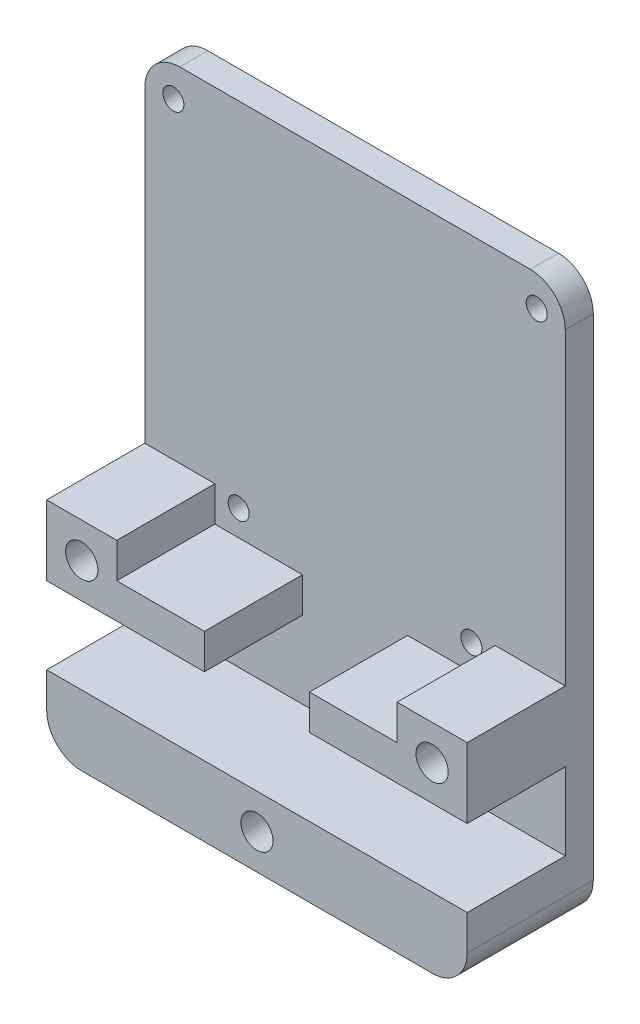
SolidWorks part; units mm, degrees
ref_plane "Plan de face" through (0, 0, 0) normal (0, 0, 1) x (1, 0, 0)
ref_plane "Plan de dessus" through (0, 0, 0) normal (0, 1, 0) x (1, 0, 0)
ref_plane "Plan de droite" through (0, 0, 0) normal (1, 0, 0) x (0, 0, -1)
sketch "Esquisse1" plane through (0, 0, 0) normal (0, 0, 1) x (1, 0, 0)
  line L0 (5, 0) -> (55, 0)
  line L1 (0, -5) -> (0, -75)
  line L2 (60, -5) -> (60, -75)
  line L3 (5, -80) -> (55, -80)
  arc A0 (0, -75) -> (5, -80) centre (5, -75) ccw
  arc A1 (55, -80) -> (60, -75) centre (55, -75) ccw
  arc A2 (60, -5) -> (55, 0) centre (55, -5) ccw
  arc A3 (0, -5) -> (5, 0) centre (5, -5) cw
  point P7 (0, -80)
  point P10 (60, -80)
  point P13 (60, 0)
  point P16 (0, 0)
  dimension "D3" = 5
  dimension "D1" = 60
  dimension "D2" = 80
extrude "Boss.-Extru.1" add sketch "Esquisse1" along normal blind 4 contours L2 A1 L3 A0 L1 A3 L0 A2
sketch "Esquisse2" plane through (0, 0, 4) normal (0, 0, 1) x (1, 0, 0)
  line L2 (5, -80) -> (55, -80)
  line L3 (5, -80) -> (55, -80)
  line L4 (0, -59) -> (60, -59)
  line L5 (0, -5) -> (0, -75) construction
  line L6 (60, -5) -> (60, -75) construction
  line L7 (0, -59) -> (22.5, -59)
  line L8 (0, -59) -> (0, -49)
  line L11 (60, -59) -> (37.5, -59)
  line L12 (60, -59) -> (60, -49)
  line L15 (0, -75) -> (0, -70)
  line L16 (0, -70) -> (60, -70)
  line L17 (60, -70) -> (60, -75)
  line L18 (60, -49) -> (50, -49)
  line L19 (50, -49) -> (50, -54)
  line L20 (50, -54) -> (37.5, -54)
  line L21 (37.5, -54) -> (37.5, -59)
  line L22 (22.5, -59) -> (22.5, -54)
  line L23 (22.5, -54) -> (10, -54)
  line L24 (10, -54) -> (10, -49)
  line L25 (10, -49) -> (0, -49)
  arc A4 (55, -80) -> (60, -75) centre (55, -75) ccw
  arc A5 (0, -75) -> (5, -80) centre (5, -75) ccw
  arc A6 (55, -80) -> (60, -75) centre (55, -75) ccw
  arc A7 (0, -75) -> (5, -80) centre (5, -75) ccw
  dimension "D2" = 10
  dimension "D3" = 10
  dimension "D4" = 10
  dimension "D5" = 90
  dimension "D6" = 10
  dimension "D7" = 10
  dimension "D8" = 11
  dimension "D9" = 5
  dimension "D10" = 5
  dimension "D11" = 15
  dimension "D12" = 22.5
  dimension "D13" = 22.5
  dimension "D1" = 0
extrude "Boss.-Extru.2" add sketch "Esquisse2" along normal blind 14
sketch "Esquisse3" plane through (0, 0, 4) normal (0, 0, 1) x (1, 0, 0)
  line L0 (10, -54) -> (50, -54) construction
  line L1 (22.5, -54) -> (10, -54) construction
  line L2 (60, 0) -> (0, 0) construction
  line L5 (22.5, -54) -> (10, -54) construction
  line L6 (60, 0) -> (60, -6.2547) construction
  line L7 (30, -54) -> (30, 0) construction
  line L8 (60, -5) -> (60, -49) construction
  line L9 (0, 0) -> (0, -7.426) construction
  line L10 (0, -5) -> (0, -49) construction
  line L11 (10, -54) -> (60, 0) construction
  line L12 (0, 0) -> (50, -54) construction
  circle A8 centre (55.9236, -4.4026) radius 1.5
  circle A9 centre (46.603, -50.3312) radius 1.5
  circle A10 centre (4.0764, -4.4026) radius 1.5
  circle A11 centre (13.397, -50.3312) radius 1.5
  dimension "D1" = 3
  dimension "D3" = 3
  dimension "D5" = 30
  dimension "D2" = 6
  dimension "D4" = 5
extrude "Enlèv. mat.-Extru.1" cut sketch "Esquisse3" against normal up to surface (4 mm away) up to face at (30, -40, 0)
sketch "Esquisse4" plane through (0, 0, 18) normal (0, 0, 1) x (1, 0, 0)
  line L0 (50, -49) -> (60, -59) construction
  line L1 (10, -49) -> (0, -59) construction
  line L2 (30, -70) -> (30, -80) construction
  line L3 (0, -70) -> (60, -70) construction
  line L4 (5, -80) -> (55, -80) construction
  circle A0 centre (55, -54) radius 2.3
  circle A1 centre (5, -54) radius 2.3
  circle A2 centre (30, -75) radius 2.3
  dimension "D1" = 4.6
  dimension "D2" = 4.6
  dimension "D3" = 4.6
extrude "Enlèv. mat.-Extru.2" cut sketch "Esquisse4" against normal blind 5.7
sketch "Esquisse5" plane through (0, -80, 0) normal (0, -1, 0) x (1, 0, 0)
  line L0 (5, 6.2839) -> (55, 6.2839) construction
  line L1 (5, 18) -> (5, 0) construction
  line L2 (55, 18) -> (55, 0) construction
  text T0 "<b>SQUIRLEBOT-1</b>" font "Century Gothic" height in points 20
extrude "Enlèv. mat.-Extru.3" cut sketch "Esquisse5" against normal blind 2
